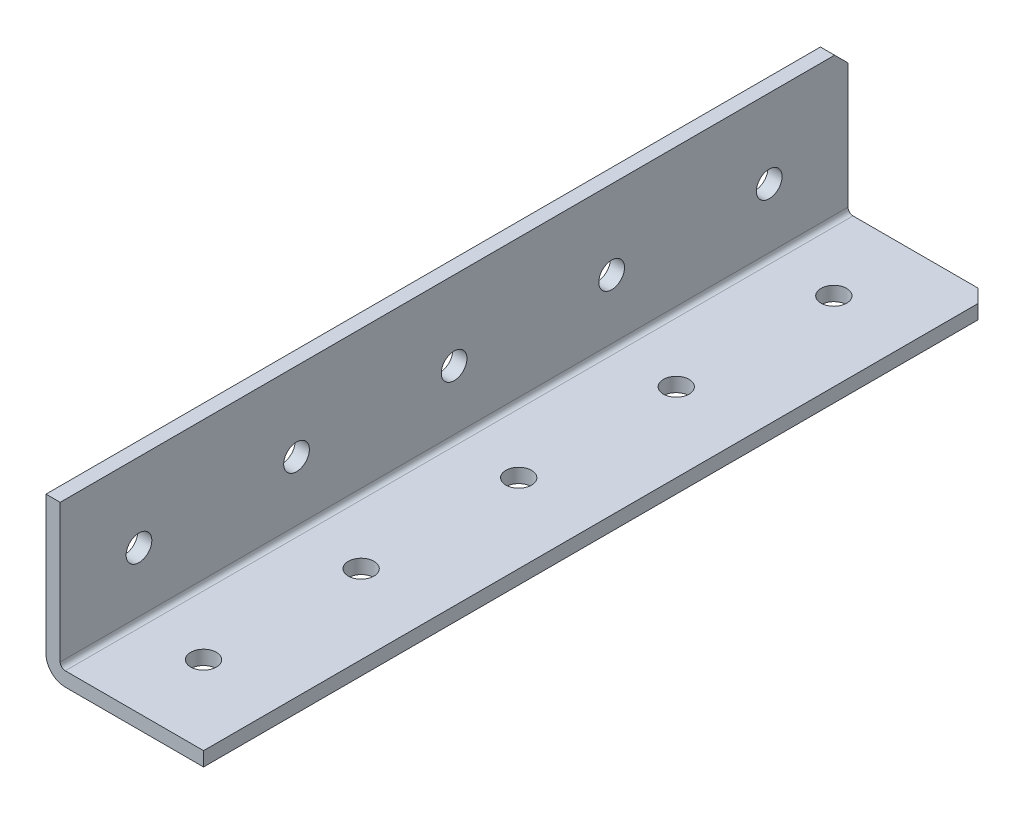
SolidWorks part; units mm, degrees
material "6061-T6 (SS)"
ref_plane "Front Plane" through (0, 0, 0) normal (0, 0, 1) x (1, 0, 0)
ref_plane "Top Plane" through (0, 0, 0) normal (0, 1, 0) x (1, 0, 0)
ref_plane "Right Plane" through (0, 0, 0) normal (1, 0, 0) x (0, 0, -1)
ref_plane "Plane1" through (0, 0, 0) normal (-1, 0, 0) x (0, -1, 0)
sketch "Sketch1" plane through (0, 0, 0) normal (-1, 0, 0) x (0, -1, 0)
  line L0 (0, 749.3) -> (-25.4, 749.3)
  line L1 (-25.4, 749.3) -> (-25.4, -749.3)
  line L2 (-25.4, -749.3) -> (0, -749.3)
  line L3 (0, -749.3) -> (0, 749.3)
extrude "Boss-Extrude1" add sketch "Sketch1" against normal blind 25.4
sketch "Sketch2" plane through (0, 0, -749.3) normal (0, 0, -1) x (-1, 0, 0)
  line L0 (-25.4, 2.286) -> (-2.286, 2.286)
  line L1 (-2.286, 2.286) -> (-2.286, 25.4)
  line L2 (-2.286, 25.4) -> (-25.4, 25.4)
  line L3 (-25.4, 25.4) -> (-25.4, 2.286)
extrude "Cut-Extrude1" cut sketch "Sketch2" against normal through all
hole_wizard "M3.5 Clearance Hole1" positions "Sketch4" profile "Sketch3" hole size "M3.5" standard "ANSI Metric"
sketch "Sketch4" plane through (0, 0, 0) normal (0, -1, 0) x (-1, 0, 0)
  point P0 (-12.7, 736.6)
  point P1 (-12.7, 711.2)
  point P2 (-12.7, 685.8)
  point P3 (-12.7, 660.4)
  point P4 (-12.7, 635)
  point P5 (-12.7, 609.6)
  point P6 (-12.7, 584.2)
  point P7 (-12.7, 558.8)
  point P8 (-12.7, 533.4)
  point P9 (-12.7, 508)
  point P10 (-12.7, 482.6)
  point P11 (-12.7, 457.2)
  point P12 (-12.7, 431.8)
  point P13 (-12.7, 406.4)
  point P14 (-12.7, 381)
  point P15 (-12.7, 355.6)
  point P16 (-12.7, 330.2)
  point P17 (-12.7, 304.8)
  point P18 (-12.7, 279.4)
  point P19 (-12.7, 254)
  point P20 (-12.7, 228.6)
  point P21 (-12.7, 203.2)
  point P22 (-12.7, 177.8)
  point P23 (-12.7, 152.4)
  point P24 (-12.7, 127)
  point P25 (-12.7, 101.6)
  point P26 (-12.7, 76.2)
  point P27 (-12.7, 50.8)
  point P28 (-12.7, 25.4)
  point P29 (-12.7, 0)
  point P30 (-12.7, -25.4)
  point P31 (-12.7, -50.8)
  point P32 (-12.7, -76.2)
  point P33 (-12.7, -101.6)
  point P34 (-12.7, -127)
  point P35 (-12.7, -152.4)
  point P36 (-12.7, -177.8)
  point P37 (-12.7, -203.2)
  point P38 (-12.7, -228.6)
  point P39 (-12.7, -254)
  point P40 (-12.7, -279.4)
  point P41 (-12.7, -304.8)
  point P42 (-12.7, -330.2)
  point P43 (-12.7, -355.6)
  point P44 (-12.7, -381)
  point P45 (-12.7, -406.4)
  point P46 (-12.7, -431.8)
  point P47 (-12.7, -457.2)
  point P48 (-12.7, -482.6)
  point P49 (-12.7, -508)
  point P50 (-12.7, -533.4)
  point P51 (-12.7, -558.8)
  point P52 (-12.7, -584.2)
  point P53 (-12.7, -609.6)
  point P54 (-12.7, -635)
  point P55 (-12.7, -660.4)
  point P56 (-12.7, -685.8)
  point P57 (-12.7, -711.2)
  point P58 (-12.7, -736.6)
sketch "Sketch3" plane through (12.7, 0, -736.6) normal (1, 0, 0) x (0, 0, -1)
  line L0 (0, 0) -> (0, 25.4)
  line L1 (0, 25.4) -> (2.0701, 25.4)
  line L2 (2.0701, 25.4) -> (2.0701, 0)
  line L5 (2.0701, 0) -> (0, 0)
  line L11 (0, -6.35) -> (0, 107.95) construction
  dimension "Thru Hole Dia." = 4.1402
  dimension "Thru Hole Depth" = 25.4
hole_wizard "M3.5 Clearance Hole2" positions "Sketch6" profile "Sketch5" hole size "M3.5" standard "ANSI Metric"
sketch "Sketch6" plane through (0, 0, 0) normal (-1, 0, 0) x (0, 0, 1)
  point P0 (711.2, 12.7)
  point P1 (736.6, 12.7)
  point P2 (685.8, 12.7)
  point P3 (660.4, 12.7)
  point P4 (635, 12.7)
  point P5 (609.6, 12.7)
  point P6 (584.2, 12.7)
  point P7 (558.8, 12.7)
  point P8 (533.4, 12.7)
  point P9 (508, 12.7)
  point P10 (482.6, 12.7)
  point P11 (457.2, 12.7)
  point P12 (431.8, 12.7)
  point P13 (406.4, 12.7)
  point P14 (381, 12.7)
  point P15 (355.6, 12.7)
  point P16 (330.2, 12.7)
  point P17 (304.8, 12.7)
  point P18 (279.4, 12.7)
  point P19 (254, 12.7)
  point P20 (228.6, 12.7)
  point P21 (203.2, 12.7)
  point P22 (177.8, 12.7)
  point P23 (152.4, 12.7)
  point P24 (127, 12.7)
  point P25 (101.6, 12.7)
  point P26 (76.2, 12.7)
  point P27 (50.8, 12.7)
  point P28 (25.4, 12.7)
  point P29 (0, 12.7)
  point P30 (-25.4, 12.7)
  point P31 (-50.8, 12.7)
  point P32 (-76.2, 12.7)
  point P33 (-101.6, 12.7)
  point P34 (-127, 12.7)
  point P35 (-152.4, 12.7)
  point P36 (-177.8, 12.7)
  point P37 (-203.2, 12.7)
  point P38 (-228.6, 12.7)
  point P39 (-254, 12.7)
  point P40 (-279.4, 12.7)
  point P41 (-304.8, 12.7)
  point P42 (-330.2, 12.7)
  point P43 (-355.6, 12.7)
  point P44 (-381, 12.7)
  point P45 (-406.4, 12.7)
  point P46 (-431.8, 12.7)
  point P47 (-457.2, 12.7)
  point P48 (-482.6, 12.7)
  point P49 (-508, 12.7)
  point P50 (-533.4, 12.7)
  point P51 (-558.8, 12.7)
  point P52 (-584.2, 12.7)
  point P53 (-609.6, 12.7)
  point P54 (-635, 12.7)
  point P55 (-660.4, 12.7)
  point P56 (-685.8, 12.7)
  point P57 (-711.2, 12.7)
  point P58 (-736.6, 12.7)
sketch "Sketch5" plane through (0, 12.7, 711.2) normal (0, 1, 0) x (0, 0, 1)
  line L0 (0, 0) -> (0, 25.4)
  line L1 (0, 25.4) -> (2.0701, 25.4)
  line L2 (2.0701, 25.4) -> (2.0701, 0)
  line L5 (2.0701, 0) -> (0, 0)
  line L11 (0, -6.35) -> (0, 107.95) construction
  dimension "Thru Hole Dia." = 4.1402
  dimension "Thru Hole Depth" = 25.4
chamfer "Chamfer1" distance 2.159 angle 45 4 edges at (25.4, 1.143, -749.3) (1.143, 25.4, -749.3) (1.143, 25.4, 749.3) (25.4, 1.143, 749.3)
fillet "Fillet1" radius 0.8128 1 edges at (2.286, 2.286, 0)
fillet "Fillet2" radius 3.0988 1 edges at (0, 0, 0)
sketch "Sketch8" plane through (0, 0, 749.3) normal (0, 0, 1) x (1, 0, 0)
  line L1 (-45.6555, -36.5704) -> (50.2275, -36.5704)
  line L2 (-45.6555, -36.5704) -> (-45.6555, 42.768)
  line L3 (-45.6555, 42.768) -> (50.2275, 42.768)
  line L4 (50.2275, -36.5704) -> (50.2275, 42.768)
  line L5 (-45.6555, -36.5704) -> (50.2275, 42.768) construction
  line L6 (-45.6555, 42.768) -> (50.2275, -36.5704) construction
  point P0 (2.286, 3.0988)
extrude "Cut-Extrude3" cut sketch "Sketch8" against normal blind 1371.6
